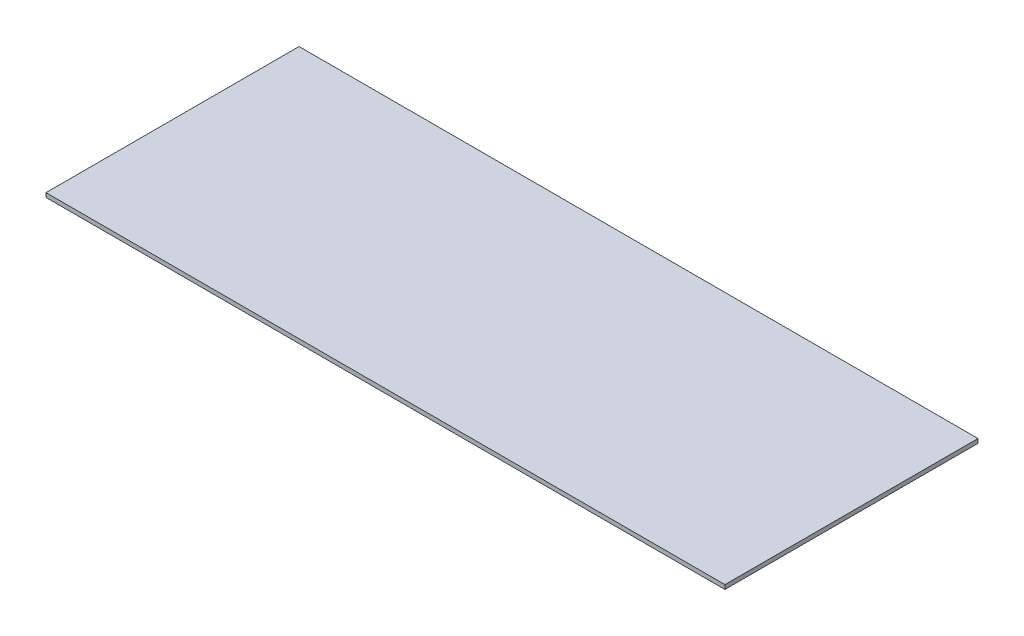
SolidWorks part; units mm, degrees
ref_plane "Front Plane" through (0, 0, 0) normal (0, 0, 1) x (1, 0, 0)
ref_plane "Top Plane" through (0, 0, 0) normal (0, 1, 0) x (1, 0, 0)
ref_plane "Right Plane" through (0, 0, 0) normal (1, 0, 0) x (0, 0, -1)
sketch "Sketch1" plane through (0, 0, 0) normal (0, 1, 0) x (1, 0, 0)
  line L1 (-165.1236, 0) -> (320.459, 0)
  line L2 (-165.1236, 0) -> (-165.1236, 181)
  line L3 (-165.1236, 181) -> (320.459, 181)
  line L4 (320.459, 0) -> (320.459, 181)
  dimension "D1" = 181
extrude "Boss-Extrude1" add sketch "Sketch1" along normal blind 3
